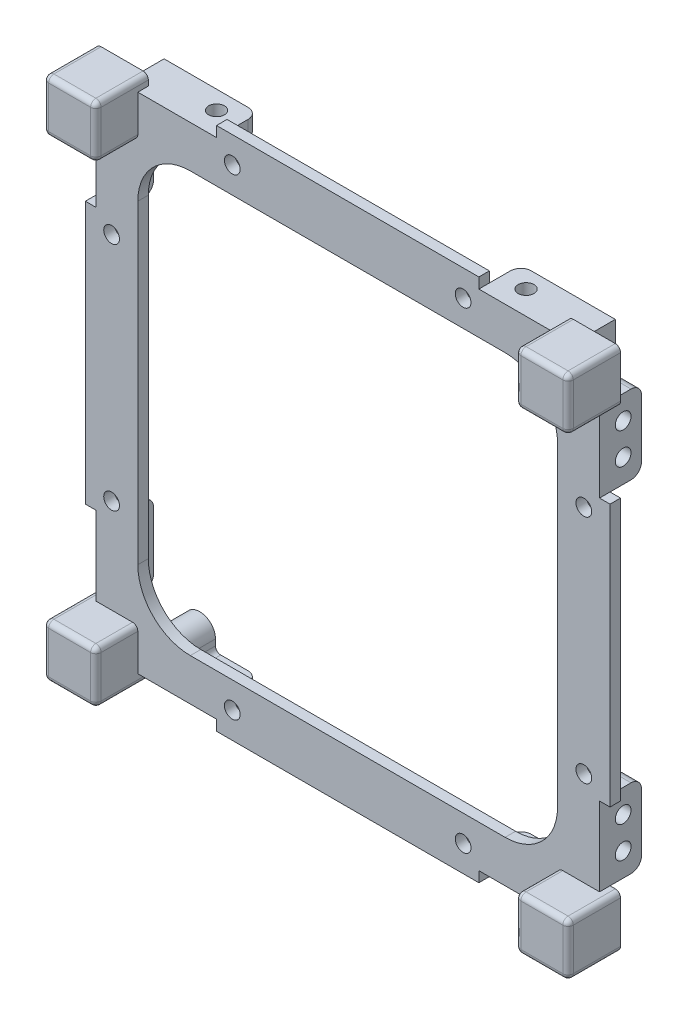
SolidWorks part; units mm, degrees
material "6061-T4 (SS)"
ref_plane "Front Plane" through (0, 0, 0) normal (0, 0, 1) x (1, 0, 0)
ref_plane "Top Plane" through (0, 0, 0) normal (0, 1, 0) x (1, 0, 0)
ref_plane "Right Plane" through (0, 0, 0) normal (1, 0, 0) x (0, 0, -1)
sketch "Sketch1" plane through (0, 0, 0) normal (0, 0, 1) x (1, 0, 0)
  line L0 (-50, 40) -> (-48, 40)
  line L1 (-49, -50) -> (-40, -50)
  line L2 (-50, -49) -> (-50, -40)
  line L3 (-49, 50) -> (-40, 50)
  line L4 (50, -49) -> (50, -40)
  line L5 (-50, -50) -> (50, 50) construction
  line L6 (-50, 50) -> (50, -50) construction
  line L7 (-30, -40) -> (30, -40)
  line L8 (-40, -30) -> (-40, 30)
  line L9 (-30, 40) -> (30, 40)
  line L10 (40, -30) -> (40, 30)
  line L11 (-40, -40) -> (40, 40) construction
  line L12 (-40, 40) -> (40, -40) construction
  line L13 (-48, 40) -> (-48, 25)
  line L14 (-48, 25) -> (-50, 25)
  line L15 (0, 50) -> (0, -50) construction
  line L16 (50, 0) -> (-50, 0) construction
  line L17 (48, 25) -> (50, 25)
  line L18 (48, 40) -> (48, 25)
  line L19 (50, 40) -> (48, 40)
  line L20 (50, -40) -> (48, -40)
  line L21 (48, -40) -> (48, -25)
  line L22 (48, -25) -> (50, -25)
  line L23 (-48, -25) -> (-50, -25)
  line L24 (-48, -40) -> (-48, -25)
  line L25 (-50, -40) -> (-48, -40)
  line L26 (50, 40) -> (50, 49)
  line L27 (-50, 40) -> (-50, 49)
  line L28 (-50, -25) -> (-50, 25)
  line L29 (50, -25) -> (50, 25)
  line L30 (-50, 22) -> (-40, 22) construction
  line L31 (-40, 50) -> (-40, 48)
  line L32 (-40, 48) -> (-25, 48)
  line L33 (-25, 48) -> (-25, 50)
  line L34 (-25, 50) -> (25, 50)
  line L35 (-22, 50) -> (-22, 40) construction
  line L36 (25, 48) -> (25, 50)
  line L37 (40, 48) -> (25, 48)
  line L38 (40, 50) -> (40, 48)
  line L39 (22, 50) -> (22, 40) construction
  line L40 (40, 50) -> (49, 50)
  line L41 (50, 22) -> (40, 22) construction
  line L42 (22, -50) -> (22, -40) construction
  line L43 (50, -22) -> (40, -22) construction
  line L44 (40, -50) -> (40, -48)
  line L45 (40, -48) -> (25, -48)
  line L46 (25, -48) -> (25, -50)
  line L47 (-22, -50) -> (-22, -40) construction
  line L48 (-25, -48) -> (-25, -50)
  line L49 (-40, -48) -> (-25, -48)
  line L50 (-40, -50) -> (-40, -48)
  line L51 (-50, -22) -> (-40, -22) construction
  line L52 (-25, -50) -> (25, -50)
  line L53 (40, -50) -> (49, -50)
  arc A0 (-49, -50) -> (-50, -49) centre (-49, -49) cw
  arc A1 (49, -50) -> (50, -49) centre (49, -49) ccw
  arc A2 (50, 49) -> (49, 50) centre (49, 49) ccw
  arc A3 (-49, 50) -> (-50, 49) centre (-49, 49) ccw
  arc A4 (-30, -40) -> (-40, -30) centre (-30, -30) cw
  arc A5 (30, -40) -> (40, -30) centre (30, -30) ccw
  arc A6 (40, 30) -> (30, 40) centre (30, 30) ccw
  arc A7 (-30, 40) -> (-40, 30) centre (-30, 30) ccw
  circle A8 centre (-45, 22) radius 1.5
  circle A9 centre (-22, 45) radius 1.5
  circle A10 centre (22, 45) radius 1.5
  circle A11 centre (45, 22) radius 1.5
  circle A12 centre (45, -22) radius 1.5
  circle A13 centre (22, -45) radius 1.5
  circle A14 centre (-22, -45) radius 1.5
  circle A15 centre (-45, -22) radius 1.5
  point P0 (0, 0)
  point P18 (0, 0)
  dimension "D2" = 1
  dimension "D3" = 10
  dimension "D9" = 3
  dimension "D1" = 100
  dimension "D4" = 10
  dimension "D5" = 15
  dimension "D6" = 2
  dimension "D7" = 10
  dimension "D8" = 100
  dimension "D10" = 28
  dimension "D11" = 10
  dimension "D12" = 28
extrude "Boss-Extrude1" add sketch "Sketch1" along normal blind 2
sketch "Sketch2" plane through (0, 0, 2) normal (0, 0, 1) x (1, 0, 0)
  line L0 (-50, 49) -> (-50, 40) construction
  line L1 (-49, 50) -> (-40, 50)
  line L2 (-50, 49) -> (-50, 40)
  line L3 (-50, 40) -> (-40, 40)
  line L4 (-40, 50) -> (-40, 40)
  line L5 (-50, 50) -> (-40, 40) construction
  line L6 (-50, 40) -> (-40, 50) construction
  line L7 (-40, 50) -> (-49, 50) construction
  line L8 (0, 50) -> (0, -50) construction
  line L9 (25, 50) -> (-25, 50) construction
  line L10 (-25, -50) -> (25, -50) construction
  line L11 (-50, 0) -> (50, 0) construction
  line L12 (-50, 25) -> (-50, -25) construction
  line L13 (50, -25) -> (50, 25) construction
  line L14 (50, 40) -> (40, 50) construction
  line L15 (50, 50) -> (40, 40) construction
  line L16 (40, 50) -> (40, 40)
  line L17 (50, 40) -> (40, 40)
  line L18 (50, 49) -> (50, 40)
  line L19 (49, 50) -> (40, 50)
  line L20 (50, -50) -> (40, -40) construction
  line L21 (50, -40) -> (40, -50) construction
  line L22 (-50, -40) -> (-40, -50) construction
  line L23 (-50, -50) -> (-40, -40) construction
  line L24 (49, -50) -> (40, -50)
  line L25 (50, -49) -> (50, -40)
  line L26 (50, -40) -> (40, -40)
  line L27 (40, -50) -> (40, -40)
  line L28 (-40, -50) -> (-40, -40)
  line L29 (-50, -40) -> (-40, -40)
  line L30 (-50, -49) -> (-50, -40)
  line L31 (-49, -50) -> (-40, -50)
  arc A0 (-49, 50) -> (-50, 49) centre (-49, 49) ccw
  arc A1 (49, 50) -> (50, 49) centre (49, 49) cw
  arc A2 (49, -50) -> (50, -49) centre (49, -49) ccw
  arc A3 (-49, -50) -> (-50, -49) centre (-49, -49) cw
  point P0 (-45, 45)
  point P31 (45, 45)
  point P46 (45, -45)
  point P47 (-45, -45)
  dimension "D3" = 1
  dimension "D1" = 10
  dimension "D2" = 10
extrude "Boss-Extrude3" add sketch "Sketch2" along normal blind 8
fillet "Fillet2" radius 1 32 edges at (-44.5, 50, 10) (-49.7071, 49.7071, 10) (-50, 44.5, 10) (-40, 50, 5) (-45, 40, 10) (-40, 45, 10) (-40, 40, 6) (-50, 40, 5) (-40, -50, 5) (-40, -45, 10) (-44.5, -50, 10) (-49.7071, -49.7071, 10) (-50, -44.5, 10) (-45, -40, 10) (-50, -40, 5) (-40, -40, 6) (50, -40, 5) (40, -50, 5) (40, -40, 6) (45, -40, 10) (50, -44.5, 10) (49.7071, -49.7071, 10) (44.5, -50, 10) (40, -45, 10) (40, 50, 5) (50, 40, 5) (40, 40, 6) (40, 45, 10) (49.7071, 49.7071, 10) (44.5, 50, 10) (50, 44.5, 10) (45, 40, 10)
sketch "Sketch6" plane through (0, 0, 0) normal (0, 0, -1) x (-1, 0, 0)
  line L0 (-43, 48) -> (-43, 42.85)
  line L1 (-45.1, -47.95) -> (45.1, -47.95) construction
  line L2 (-45.1, -47.95) -> (-45.1, 47.95) construction
  line L3 (-45.1, 47.95) -> (45.1, 47.95) construction
  line L4 (45.1, -47.95) -> (45.1, 47.95) construction
  line L5 (-45.1, -47.95) -> (45.1, 47.95) construction
  line L6 (-45.1, 47.95) -> (45.1, -47.95) construction
  line L7 (-37, 42.85) -> (-37, 44)
  line L8 (-36, 45) -> (-25, 45)
  line L9 (-25, 45) -> (-25, 48)
  line L10 (-25, 48) -> (-43, 48)
  line L11 (0, 0) -> (0, 47.95) construction
  line L12 (0, 0) -> (-45.1, 0) construction
  line L13 (25, 48) -> (25, 45)
  line L14 (25, 45) -> (36, 45)
  line L15 (37, 44) -> (37, 42.85)
  line L16 (25, 48) -> (43, 48)
  line L17 (43, 48) -> (43, 42.85)
  line L18 (-40.4, -48) -> (-40.4, -42.85)
  line L19 (-40.4, -48) -> (-25, -48)
  line L20 (-25, -48) -> (-25, -45)
  line L21 (-25, -45) -> (-33.4, -45)
  line L22 (-34.4, -44) -> (-34.4, -42.85)
  line L23 (25, -48) -> (25, -45)
  line L24 (25, -45) -> (32.2, -45)
  line L25 (33.2, -44) -> (33.2, -42.85)
  line L26 (39.2, -42.85) -> (39.2, -48)
  line L27 (39.2, -48) -> (25, -48)
  line L28 (40, -48) -> (25, -48) construction
  line L29 (-50, 25) -> (-48, 25) construction
  line L30 (-48, 40) -> (-45, 40)
  line L31 (-48, 40) -> (-48, 25)
  line L32 (-48, 25) -> (-45, 25)
  line L33 (-45, 40) -> (-45, 25)
  line L34 (48, 25) -> (50, 25) construction
  line L35 (48, 40) -> (45, 40)
  line L36 (48, 40) -> (48, 25)
  line L37 (48, 25) -> (45, 25)
  line L38 (45, 40) -> (45, 25)
  line L39 (-49, -40) -> (-48, -40) construction
  line L40 (-48, -25) -> (-45, -25)
  line L41 (-48, -25) -> (-48, -40)
  line L42 (-48, -40) -> (-45, -40)
  line L43 (-45, -25) -> (-45, -40)
  line L44 (48, -40) -> (49, -40) construction
  line L45 (48, -25) -> (45, -25)
  line L46 (48, -25) -> (48, -40)
  line L47 (48, -40) -> (45, -40)
  line L48 (45, -25) -> (45, -40)
  circle A0 centre (-40, 42.85) radius 1.5
  circle A1 centre (-37.4, -42.85) radius 1.5
  circle A2 centre (40, 42.85) radius 1.5
  circle A3 centre (36.2, -42.85) radius 1.5
  arc A4 (-43, 42.85) -> (-37, 42.85) centre (-40, 42.85) ccw
  arc A5 (-37, 44) -> (-36, 45) centre (-36, 44) cw
  arc A6 (37, 42.85) -> (43, 42.85) centre (40, 42.85) ccw
  arc A7 (37, 44) -> (36, 45) centre (36, 44) ccw
  arc A8 (-40.4, -42.85) -> (-34.4, -42.85) centre (-37.4, -42.85) cw
  arc A9 (-33.4, -45) -> (-34.4, -44) centre (-33.4, -44) cw
  arc A10 (33.2, -42.85) -> (39.2, -42.85) centre (36.2, -42.85) cw
  arc A11 (32.2, -45) -> (33.2, -44) centre (32.2, -44) ccw
  point P0 (0, 0)
  dimension "D3" = 3
  dimension "D10" = 3
  dimension "D11" = 1
  dimension "D13" = 1
  dimension "D14" = 3
  dimension "D15" = 1
  dimension "D18" = 3
  dimension "D19" = 1
  dimension "D1" = 95.9
  dimension "D2" = 90.2
  dimension "D4" = 85.1
  dimension "D5" = 5.1
  dimension "D6" = 90.8
  dimension "D7" = 8.9
  dimension "D8" = 82.5
  dimension "D9" = 5.1
  dimension "D12" = 3
  dimension "D16" = 3
  dimension "D17" = 3
  dimension "D20" = 3
extrude "Boss-Extrude5" add sketch "Sketch6" along normal blind 6
fillet "Fillet3" radius 2 12 edges at (46.5, -40, -6) (46.5, -25, -6) (-46.5, -40, -6) (-46.5, -25, -6) (-46.5, 25, -6) (-46.5, 40, -6) (-25, 46.5, -6) (25, 46.5, -6) (46.5, 25, -6) (46.5, 40, -6) (-25, -46.5, -6) (25, -46.5, -6)
sketch "Sketch7" plane through (0, 0, 0) normal (1, 0, 0) x (0, 0, -1)
  line L0 (6, 38) -> (6, 27) construction
  line L1 (4, 40) -> (0, 40) construction
  line L2 (0, 0) -> (9.3897, 0) construction
  circle A0 centre (2.5, 35.5) radius 1.5
  circle A1 centre (2.5, 29.5) radius 1.5
  circle A2 centre (2.5, -29.5) radius 1.5
  circle A3 centre (2.5, -35.5) radius 1.5
  dimension "D1" = 3
  dimension "D2" = 3.5
  dimension "D3" = 4.5
  dimension "D4" = 6
extrude "Cut-Extrude1" cut sketch "Sketch7" against normal through all and the other way through all
sketch "Sketch8" plane through (0, 0, 0) normal (0, 1, 0) x (1, 0, 0)
  line L0 (-43, 6) -> (-27, 6) construction
  line L1 (-25, 4) -> (-25, 0) construction
  line L2 (25, 4) -> (25, 0) construction
  circle A0 centre (-29.5, 2.5) radius 1.5
  circle A1 centre (29.5, 2.5) radius 1.5
  dimension "D1" = 3
  dimension "D2" = 3.5
  dimension "D3" = 4.5
  dimension "D4" = 4.5
extrude "Cut-Extrude2" cut sketch "Sketch8" against normal through all and the other way through all
